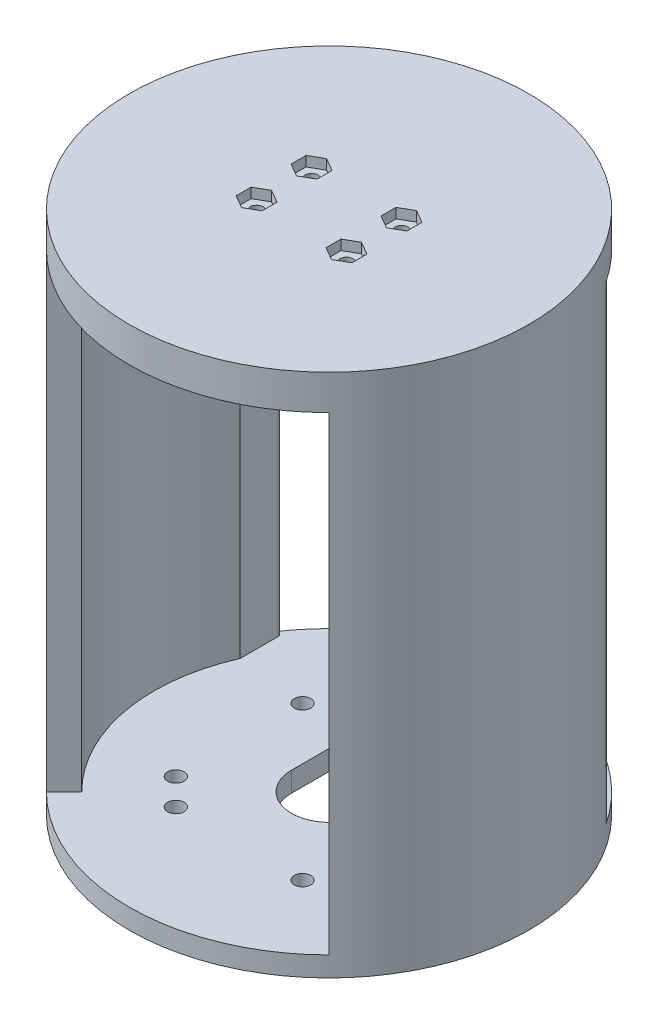
SolidWorks part; units mm, degrees
ref_plane "Front Plane" through (0, 0, 0) normal (0, 0, 1) x (1, 0, 0)
ref_plane "Top Plane" through (0, 0, 0) normal (0, 1, 0) x (1, 0, 0)
ref_plane "Right Plane" through (0, 0, 0) normal (1, 0, 0) x (0, 0, -1)
sketch "Sketch1" plane through (0, 0, 0) normal (0, 1, 0) x (1, 0, 0)
  line L1 (576.4323, -817.1449) -> (7.5, -10.6319) construction
  line L2 (-576.4323, -817.1449) -> (-7.5, -10.6319) construction
  line L3 (-817.1449, -576.4323) -> (-7.5, -5.2907) construction
  line L4 (817.1449, -576.4323) -> (7.5, -5.2907) construction
  line L5 (-6.1286, 4.3232) -> (-40857.2449, 28821.6158) construction
  line L7 (-7.5, 0) -> (-7.5, -39.2906)
  line L9 (7.5, 0) -> (7.5, -39.2906)
  line L10 (-4.3232, 6.1286) -> (-12.6815, 17.9772) construction
  line L11 (0, 7.5) -> (0, 50000) construction
  line L12 (4.3232, 6.1286) -> (12.6815, 17.9772) construction
  line L13 (6.1286, 4.3232) -> (27.2941, 19.2539) construction
  arc A0 (7.5, -39.2906) -> (-7.5, -39.2906) centre (0, 0) ccw
  arc A1 (7.5, -20.6821) -> (-7.5, -20.6821) centre (0, 0) ccw construction
  circle A2 centre (-17.9772, 12.6815) radius 1.65
  circle A3 centre (-12.6815, 17.9772) radius 1.65
  circle A4 centre (12.6815, 17.9772) radius 1.65
  circle A5 centre (17.9772, 12.6815) radius 1.65
  circle A6 centre (17.9772, -12.6815) radius 1.65
  circle A7 centre (12.6815, -17.9772) radius 1.65
  circle A8 centre (-12.6815, -17.9772) radius 1.65
  circle A9 centre (-17.9772, -12.6815) radius 1.65
  arc A11 (7.5, 0) -> (-7.5, 0) centre (0, 0) ccw
  dimension "D1" = 80
  dimension "D2" = 22
  dimension "D7" = 3.3
  dimension "D8" = 3.3
  dimension "D9" = 4
  dimension "D4" = 70.4
  dimension "D5" = 19.6
  dimension "D6" = 19.6
  dimension "D11" = 15
extrude "Boss-Extrude1" add sketch "Sketch1" along normal blind 4
sketch "Sketch2" plane through (0, 4, 0) normal (0, 1, 0) x (1, 0, 0)
  line L3 (-24.7487, -24.7487) -> (-28.2843, -28.2843)
  line L4 (24.7487, -24.7487) -> (28.2843, -28.2843)
  line L7 (-32, 21.7991) -> (-32, 14.1774)
  line L9 (32, 21.7991) -> (32, 14.1774)
  arc A0 (-33.2824, 22.1874) -> (-28.2843, -28.2843) centre (0, 0) ccw
  arc A1 (-32, 14.1774) -> (-24.7487, -24.7487) centre (0, 0) ccw
  arc A2 (28.2843, -28.2843) -> (33.2824, 22.1874) centre (0, 0) ccw
  arc A3 (24.7487, -24.7487) -> (32, 14.1774) centre (0, 0) ccw
  arc A4 (32, 21.7991) -> (33.2824, 22.1874) centre (32.7, 21.7991) cw
  arc A5 (-32, 21.7991) -> (-33.2824, 22.1874) centre (-32.7, 21.7991) ccw
  point P7 (0, 0)
  point P9 (0, 0)
  point P14 (0, 22.1264)
  dimension "D1" = 70
  dimension "D2" = 0.7
extrude "Boss-Extrude2" add sketch "Sketch2" along normal blind 94
sketch "Sketch3" plane through (0, 98, 0) normal (0, 1, 0) x (1, 0, 0)
  circle A0 centre (0, 0) radius 40
extrude "Boss-Extrude3" add sketch "Sketch3" along normal blind 7
sketch "Sketch4" plane through (0, 98, 0) normal (0, -1, 0) x (1, 0, 0)
  line L1 (9, -5.5) -> (-9, -5.5) construction
  line L2 (9, -5.5) -> (9, 5.5) construction
  line L3 (9, 5.5) -> (-9, 5.5) construction
  line L4 (-9, -5.5) -> (-9, 5.5) construction
  line L5 (9, -5.5) -> (-9, 5.5) construction
  line L6 (9, 5.5) -> (-9, -5.5) construction
  circle A0 centre (9, -5.5) radius 1.3
  circle A1 centre (-9, -5.5) radius 1.3
  circle A2 centre (9, 5.5) radius 1.3
  circle A3 centre (-9, 5.5) radius 1.3
  point P0 (0, 0)
  dimension "D3" = 2.6
  dimension "D4" = 2.6
  dimension "D5" = 2.6
  dimension "D6" = 2.6
  dimension "D1" = 11
  dimension "D2" = 18
extrude "Cut-Extrude1" cut sketch "Sketch4" against normal blind 22
sketch "Sketch5" plane through (0, 98, 0) normal (0, -1, 0) x (1, 0, 0)
  line L1 (11.5, -8) -> (-11.5, -8)
  line L2 (11.5, -8) -> (11.5, 21)
  line L3 (11.5, 21) -> (-11.5, 21)
  line L4 (-11.5, -8) -> (-11.5, 21)
  line L5 (11.5, -8) -> (-11.5, 21) construction
  line L6 (11.5, 21) -> (-11.5, -8) construction
  circle A0 centre (9, -5.5) radius 1.3 construction
  point P0 (0, 6.5)
  dimension "D2" = 2.5
  dimension "D3" = 2.5
  dimension "D1" = 23
  dimension "D4" = 29
extrude "Cut-Extrude2" cut sketch "Sketch5" against normal blind 1.6
sketch "Sketch6" plane through (0, 99.6, 0) normal (0, -1, 0) x (1, 0, 0)
  line L0 (11.5, 21) -> (-11.5, 21) construction
  line L1 (-3, 8.9) -> (4.5, 8.9)
  line L2 (-10, 14.5) -> (10, 14.5)
  line L3 (-10, 14.5) -> (-10, 19)
  line L4 (-10, 19) -> (10, 19)
  line L5 (10, 14.5) -> (10, 19)
  line L6 (-10, 14.5) -> (10, 19) construction
  line L7 (-10, 19) -> (10, 14.5) construction
  line L8 (-3, 8.9) -> (-3, 11)
  line L9 (-3, 11) -> (4.5, 11)
  line L10 (4.5, 8.9) -> (4.5, 11)
  line L11 (-3, 8.9) -> (4.5, 11) construction
  line L12 (-3, 11) -> (4.5, 8.9) construction
  line L13 (-11.5, 21) -> (-11.5, -8) construction
  line L14 (-11.5, 21) -> (-11.5, -8) construction
  point P0 (0.75, 9.95)
  point P1 (0, 16.75)
  dimension "D1" = 20
  dimension "D2" = 4.5
  dimension "D3" = 2
  dimension "D4" = 1.5
  dimension "D5" = 3.5
  dimension "D6" = 2.1
  dimension "D7" = 7.5
  dimension "D8" = 8.5
extrude "Cut-Extrude3" cut sketch "Sketch6" against normal blind 4
sketch "Sketch7" plane through (0, 105, 0) normal (0, 1, 0) x (1, 0, 0)
  line L1 (9, -8.5) -> (11.5981, -7)
  line L2 (11.5981, -7) -> (11.5981, -4)
  line L3 (11.5981, -4) -> (9, -2.5)
  line L4 (9, -2.5) -> (6.4019, -4)
  line L5 (6.4019, -4) -> (6.4019, -7)
  line L6 (6.4019, -7) -> (9, -8.5)
  line L7 (-9, 2.5) -> (-6.4019, 4)
  line L8 (-6.4019, 4) -> (-6.4019, 7)
  line L9 (-6.4019, 7) -> (-9, 8.5)
  line L10 (-9, 8.5) -> (-11.5981, 7)
  line L11 (-11.5981, 7) -> (-11.5981, 4)
  line L12 (-11.5981, 4) -> (-9, 2.5)
  line L13 (-9, -8.5) -> (-6.4019, -7)
  line L14 (-6.4019, -7) -> (-6.4019, -4)
  line L15 (-6.4019, -4) -> (-9, -2.5)
  line L16 (-9, -2.5) -> (-11.5981, -4)
  line L17 (-11.5981, -4) -> (-11.5981, -7)
  line L18 (-11.5981, -7) -> (-9, -8.5)
  line L19 (9, 2.5) -> (11.5981, 4)
  line L20 (11.5981, 4) -> (11.5981, 7)
  line L21 (11.5981, 7) -> (9, 8.5)
  line L22 (9, 8.5) -> (6.4019, 7)
  line L23 (6.4019, 7) -> (6.4019, 4)
  line L24 (6.4019, 4) -> (9, 2.5)
  circle A0 centre (9, -5.5) radius 2.5981 construction
  circle A1 centre (-9, 5.5) radius 2.5981 construction
  circle A2 centre (-9, -5.5) radius 2.5981 construction
  circle A3 centre (9, 5.5) radius 2.5981 construction
  dimension "D1" = 6
  dimension "D2" = 6
  dimension "D3" = 6
  dimension "D4" = 6
extrude "Cut-Extrude4" cut sketch "Sketch7" against normal blind 2
sketch "Sketch8" plane through (0, 0, 0) normal (0, -1, 0) x (1, 0, 0)
  line L1 (-7.9355, -8.3034) -> (8.1458, -8.3034)
  line L2 (-7.9355, -8.3034) -> (-7.9355, 39.2049)
  line L4 (8.1458, -8.3034) -> (8.1458, 39.1618)
  arc A0 (8.1458, 39.1618) -> (-7.9355, 39.2049) centre (0, 0) ccw
extrude "Boss-Extrude4" add sketch "Sketch8" against normal blind 4
sketch "Sketch9" plane through (0, 0, 0) normal (0, -1, 0) x (1, 0, 0)
  line L2 (-7.5, 0) -> (-7.5, -42.5682)
  line L3 (-7.5, -42.5682) -> (7.5, -42.5682)
  line L4 (7.5, 0) -> (7.5, -42.5682)
  arc A0 (7.5, 0) -> (-7.5, 0) centre (0, 0) ccw
  dimension "D1" = 15
extrude "Cut-Extrude5" cut sketch "Sketch9" against normal blind 4
